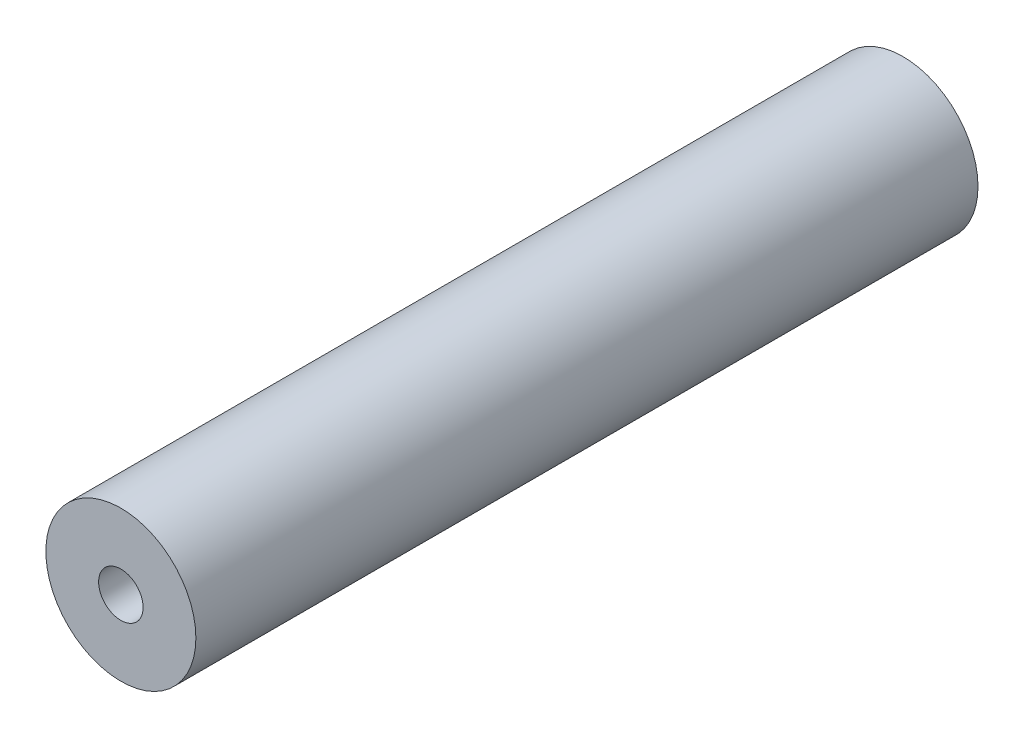
SolidWorks part; units mm, degrees
material "6061-T6 (SS)"
ref_plane "Front Plane" through (0, 0, 0) normal (0, 0, 1) x (1, 0, 0)
ref_plane "Top Plane" through (0, 0, 0) normal (0, 1, 0) x (1, 0, 0)
ref_plane "Right Plane" through (0, 0, 0) normal (1, 0, 0) x (0, 0, -1)
sketch "Sketch1" plane through (0, 0, 0) normal (0, 0, 1) x (1, 0, 0)
  circle A0 centre (0, 0) radius 6.4
  dimension "D1" = 12.8
extrude "Boss-Extrude1" add sketch "Sketch1" along normal blind 66.73
hole_wizard "#10-24 Tapped Hole1" positions "Sketch2" profile "Sketch3" tap size "#10-24" standard "ANSI Inch"
sketch "Sketch2" plane through (0, 0, 0) normal (0, 0, -1) x (-1, 0, 0)
  point P0 (0, 0)
sketch "Sketch3" plane through (0, 0, 0) normal (1, 0, 0) x (0, 1, 0)
  line L0 (0, 0) -> (0, 13.9708)
  line L1 (0, 13.9708) -> (1.8986, 12.83)
  line L2 (1.8986, 12.83) -> (1.8986, 0)
  line L5 (1.8986, 0) -> (0, 0)
  line L10 (0, 13.9708) -> (-1.8987, 12.83) construction
  line L11 (0, -6.35) -> (0, 107.95) construction
  dimension "Tap Drill Dia." = 3.7973
  dimension "Tap Drill Depth" = 12.83
  dimension "Drill Angle" = 118
hole_wizard "#10-24 Tapped Hole2" positions "Sketch4" profile "Sketch5" tap size "#10-24" standard "ANSI Inch"
sketch "Sketch4" plane through (0, 0, 66.73) normal (0, 0, 1) x (1, 0, 0)
  point P0 (0, 0)
sketch "Sketch5" plane through (0, 0, 66.73) normal (1, 0, 0) x (0, -1, 0)
  line L0 (0, 0) -> (0, 13.9708)
  line L1 (0, 13.9708) -> (1.8986, 12.83)
  line L2 (1.8986, 12.83) -> (1.8986, 0)
  line L5 (1.8986, 0) -> (0, 0)
  line L10 (0, 13.9708) -> (-1.8987, 12.83) construction
  line L11 (0, -6.35) -> (0, 107.95) construction
  dimension "Tap Drill Dia." = 3.7973
  dimension "Tap Drill Depth" = 12.83
  dimension "Drill Angle" = 118
